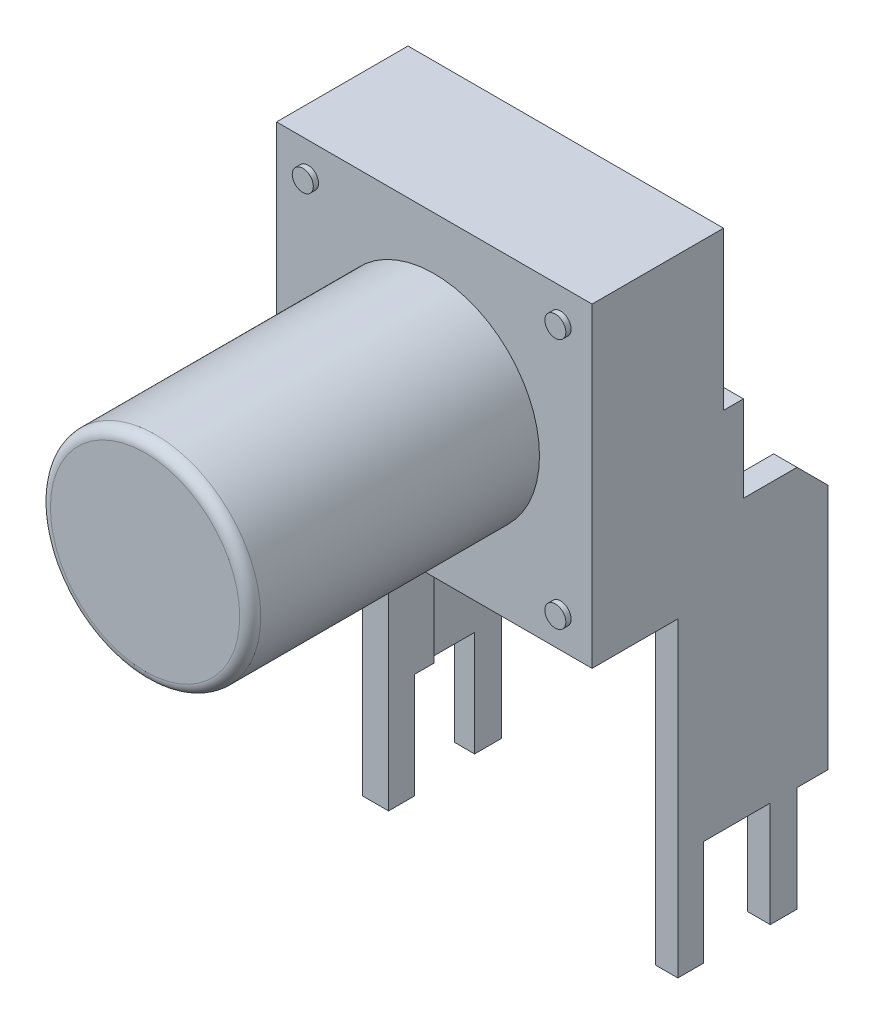
SolidWorks part; units mm, degrees
ref_plane "Front Plane" through (0, 0, 0) normal (0, 0, 1) x (1, 0, 0)
ref_plane "Top Plane" through (0, 0, 0) normal (0, 1, 0) x (1, 0, 0)
ref_plane "Right Plane" through (0, 0, 0) normal (1, 0, 0) x (0, 0, -1)
sketch "Sketch1" plane through (0, 0, 0) normal (0, 0, 1) x (1, 0, 0)
  line L1 (0, 0) -> (6, 0)
  line L2 (0, 0) -> (0, 6)
  line L3 (0, 6) -> (6, 6)
  line L4 (6, 0) -> (6, 6)
  dimension "D1" = 6
  dimension "D2" = 6
extrude "Boss-Extrude1" add sketch "Sketch1" along normal blind 2.5
sketch "Sketch2" plane through (0, 0, 2.5) normal (0, 0, 1) x (1, 0, 0)
  circle A0 centre (3, 3) radius 2
  dimension "D1" = 4
extrude "Boss-Extrude2" add sketch "Sketch2" along normal blind 5.5 separate body
sketch "Sketch3" plane through (0, 0, 2.5) normal (0, 0, 1) x (1, 0, 0)
  line L0 (3, 6) -> (3, -3.5202) construction
  line L1 (6, 6) -> (0, 6) construction
  line L2 (3, 3) -> (7.5099, 3) construction
  circle A0 centre (0.5986, 0.613) radius 0.2
  circle A1 centre (5.4014, 0.613) radius 0.2
  circle A2 centre (5.4014, 5.387) radius 0.2
  circle A3 centre (0.5986, 5.387) radius 0.2
  point P9 (0.6909, 0.6912)
  point P10 (0.8029, 0.42)
  point P11 (0.5986, 0.613)
  point P12 (0, 0)
  dimension "D1" = 0.4
extrude "Boss-Extrude3" add sketch "Sketch3" along normal blind 0.1
sketch "Sketch4" plane through (6, 0, 0) normal (1, 0, 0) x (0, 0, -1)
  line L0 (-2.5, 3) -> (0.3783, 3)
  line L1 (-2.5, 0) -> (-2.5, 6) construction
  line L2 (0.3783, 3) -> (0.3783, 1.3626)
  line L3 (0.3783, 1.3626) -> (1.398, 1.3626)
  line L4 (1.398, 1.3626) -> (1.985, 0.7755)
  line L5 (1.985, 0.7755) -> (1.985, -3.9119)
  line L6 (1.985, -3.9119) -> (1.398, -3.9119)
  line L7 (1.398, -3.9119) -> (1.398, -5.9142)
  line L8 (1.398, -5.9142) -> (0.8881, -5.9142)
  line L9 (0.8881, -5.9142) -> (0.8881, -3.9119)
  line L10 (0.8881, -3.9119) -> (-0.3794, -3.9119)
  line L11 (-0.3794, -3.9119) -> (-0.3794, -5.9142)
  line L12 (-0.3794, -5.9142) -> (-0.8688, -5.9142)
  line L13 (-0.8688, -5.9142) -> (-0.8688, 0)
  line L14 (-2.5, 0) -> (0, 0) construction
  line L15 (-0.8688, 0) -> (-2.5, 0)
  line L16 (-2.5, 0) -> (-2.5, 3)
extrude "Boss-Extrude4" add sketch "Sketch4" against normal up to vertex (6 mm away)
sketch "Sketch5" plane through (0, 6, 0) normal (0, 1, 0) x (1, 0, 0)
  line L0 (6, 0) -> (0, 0) construction
  line L1 (0.3779, 0) -> (5.5559, 0)
  line L2 (0.3779, 0) -> (0.3779, 4.1302)
  line L3 (0.3779, 4.1302) -> (5.5559, 4.1302)
  line L4 (5.5559, 0) -> (5.5559, 4.1302)
extrude "Cut-Extrude1" cut sketch "Sketch5" against normal through all both and the other way through all
sketch "Sketch6" plane through (0, 0, 0.8688) normal (0, 0, 1) x (1, 0, 0)
  line L0 (0, 0) -> (6, 0) construction
  line L1 (0.4987, 0) -> (5.5708, 0)
  line L2 (0.4987, 0) -> (0.4987, -6.6793)
  line L3 (0.4987, -6.6793) -> (5.5708, -6.6793)
  line L4 (5.5708, 0) -> (5.5708, -6.6793)
extrude "Cut-Extrude2" cut sketch "Sketch6" against normal through all both and the other way through all
fillet "Fillet1" radius 0.2 1 edges at (5, 3, 8)
